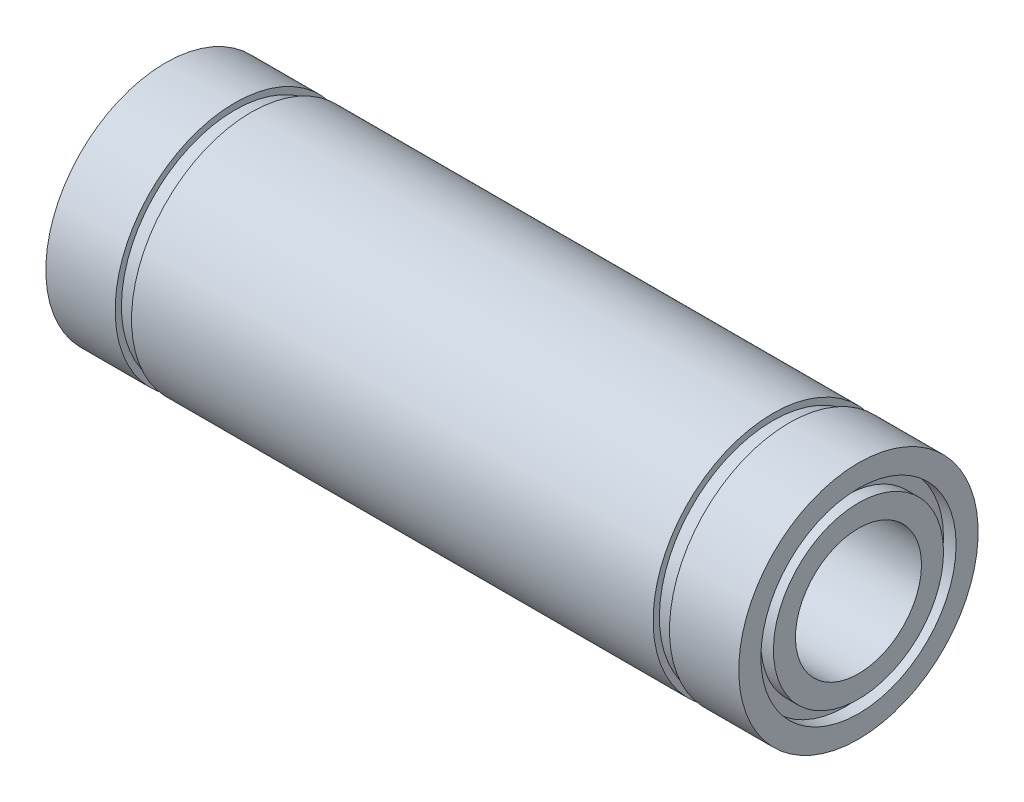
SolidWorks part; units mm, degrees
material "Ст3сп ГОСТ 535-2005"
ref_plane "Plano frontal" through (0, 0, 0) normal (0, 0, 1) x (1, 0, 0)
ref_plane "Plano superior" through (0, 0, 0) normal (0, 1, 0) x (1, 0, 0)
ref_plane "Plano direito" through (0, 0, 0) normal (1, 0, 0) x (0, 0, -1)
sketch "Esboço1" plane through (0, 0, 0) normal (0, 0, 1) x (1, 0, 0)
  line L0 (-27.5, 9.5) -> (-22, 9.5)
  line L1 (-22, 9.5) -> (-22, 9)
  line L2 (-22, 9) -> (-20.7, 9)
  line L3 (-20.7, 9) -> (-20.7, 9.5)
  line L4 (-20.7, 9.5) -> (20.7, 9.5)
  line L5 (20.7, 9.5) -> (20.7, 9)
  line L6 (20.7, 9) -> (22, 9)
  line L7 (22, 9) -> (22, 9.5)
  line L8 (22, 9.5) -> (27.5, 9.5)
  line L9 (27.5, 9.5) -> (27.5, 7.75)
  line L10 (27.5, 5) -> (-27.5, 5)
  line L11 (-27.5, 5) -> (-27.5, 6.75)
  line L12 (0, 5) -> (0, 0) construction
  line L13 (0, 0) -> (-86.5, 0) construction
  line L14 (-27.5, 7.75) -> (-27.5, 9.5)
  line L15 (-27.5, 7.75) -> (-26.5, 7.75)
  line L16 (27.5, 6.75) -> (27.5, 5)
  line L17 (-26.5, 7.75) -> (-26.5, 6.75)
  line L18 (-26.5, 6.75) -> (-27.5, 6.75)
  line L19 (27.5, 7.75) -> (26.5, 7.75)
  line L21 (27.5, 6.75) -> (26.5, 6.75)
  line L22 (26.5, 7.75) -> (26.5, 6.75)
  dimension "D1" = 55
  dimension "D2" = 44
  dimension "D3" = 1.3
  dimension "D4" = 10
  dimension "D5" = 19
  dimension "D6" = 18
  dimension "D7" = 1
  dimension "D8" = 1
  dimension "D9" = 1
  dimension "D10" = 1
revolve "Revolução1" add sketch "Esboço1" angle 360 about L13
